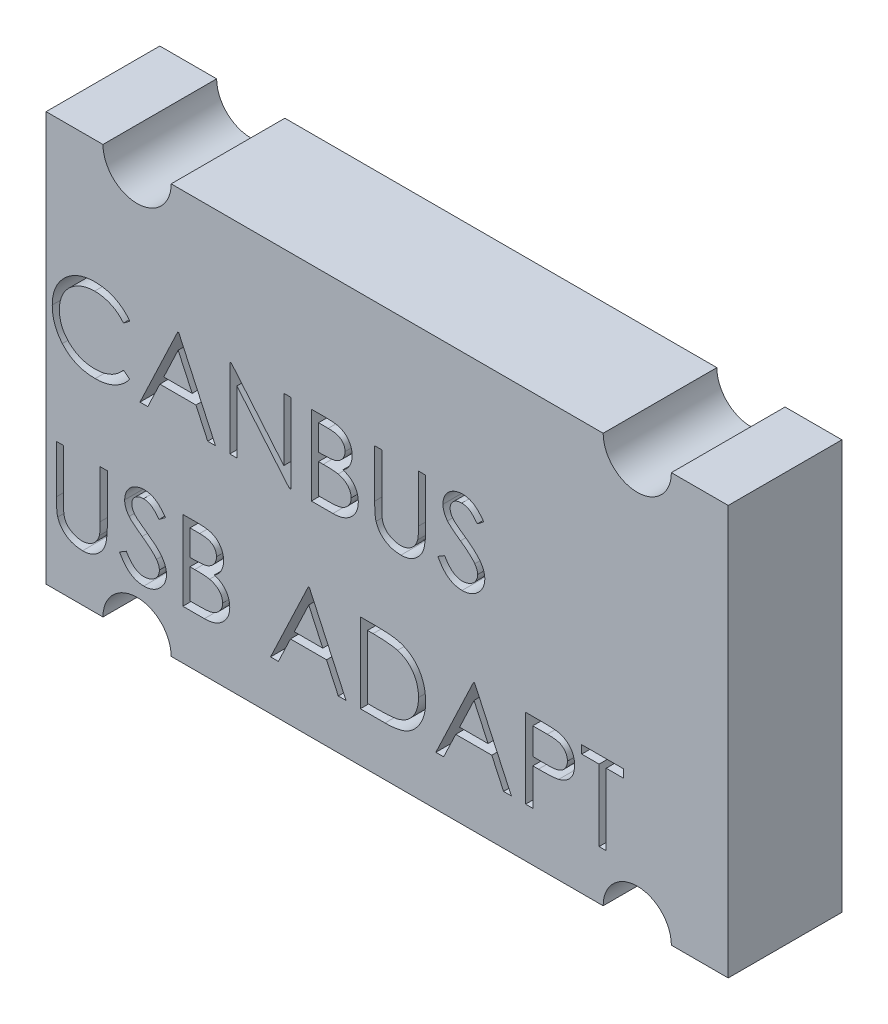
SolidWorks part; units mm, degrees
ref_plane "Front Plane" through (0, 0, 0) normal (0, 0, 1) x (1, 0, 0)
ref_plane "Top Plane" through (0, 0, 0) normal (0, 1, 0) x (1, 0, 0)
ref_plane "Right Plane" through (0, 0, 0) normal (1, 0, 0) x (0, 0, -1)
sketch "Sketch1" plane through (0, 0, 0) normal (0, 0, 1) x (1, 0, 0)
  line L0 (5.5, 18) -> (24.5, 18)
  line L1 (0, 0) -> (2.5, 0)
  line L2 (0, 0) -> (0, 18)
  line L3 (0, 18) -> (2.5, 18)
  line L4 (30, 0) -> (30, 18)
  line L5 (27.5, 18) -> (30, 18)
  line L6 (27.5, 0) -> (30, 0)
  line L7 (5.5, 0) -> (24.5, 0)
  arc A0 (5.5, 0) -> (2.5, 0) centre (4, 0) ccw
  arc A1 (27.5, 0) -> (24.5, 0) centre (26, 0) ccw
  arc A2 (2.5, 18) -> (5.5, 18) centre (4, 18) ccw
  arc A3 (24.5, 18) -> (27.5, 18) centre (26, 18) ccw
  dimension "D3" = 3
  dimension "D4" = 3
  dimension "D5" = 3
  dimension "D6" = 3
  dimension "D1" = 18
  dimension "D2" = 30
  dimension "D7" = 4
  dimension "D8" = 4
  dimension "D9" = 4
  dimension "D10" = 4
extrude "Boss-Extrude1" add sketch "Sketch1" along normal blind 5
sketch "Sketch2" plane through (0, 0, 5) normal (0, 0, 1) x (1, 0, 0)
  line L0 (0, 9) -> (30, 9) construction
  line L1 (0, 18) -> (0, 0) construction
  line L2 (30, 0) -> (30, 18) construction
  text T0 "CANBUS\r\nUSB ADAPT"
extrude "Cut-Extrude1" cut sketch "Sketch2" against normal through all
